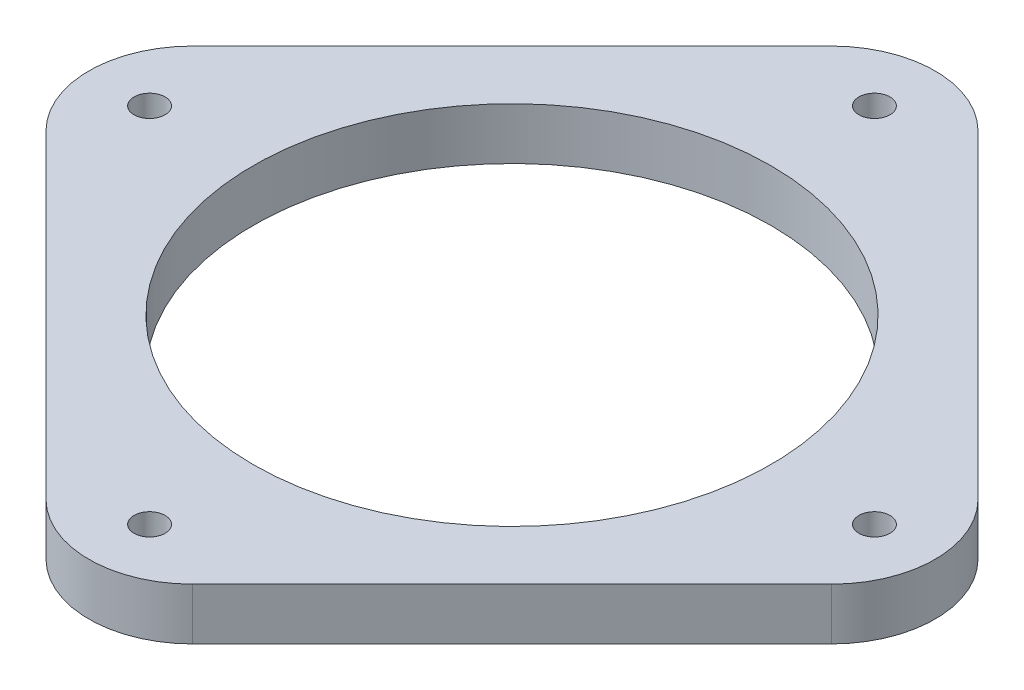
SolidWorks part; units mm, degrees
ref_plane "Alzado" through (0, 0, 0) normal (0, 0, 1) x (1, 0, 0)
ref_plane "Planta" through (0, 0, 0) normal (0, 1, 0) x (1, 0, 0)
ref_plane "Vista lateral" through (0, 0, 0) normal (1, 0, 0) x (0, 0, -1)
sketch "Croquis1" plane through (0, 0, 0) normal (0, 1, 0) x (1, 0, 0)
  line L0 (0, 0) -> (-45, 0) construction
  line L1 (-37.9289, -7.0711) -> (-7.0711, -37.9289)
  line L2 (7.0711, -37.9289) -> (37.9289, -7.0711)
  line L3 (37.9289, 7.0711) -> (7.0711, 37.9289)
  line L4 (-7.0711, 37.9289) -> (-37.9289, 7.0711)
  line L5 (0, 0) -> (35, 0) construction
  circle A0 centre (0, 0) radius 25
  circle A1 centre (0, 0) radius 31.8198 construction
  circle A2 centre (35, 0) radius 1.5
  arc A3 (-7.0711, -37.9289) -> (7.0711, -37.9289) centre (0, -30.8579) ccw
  arc A4 (-37.9289, -7.0711) -> (-37.9289, 7.0711) centre (-30.8579, 0) cw
  arc A5 (7.0711, 37.9289) -> (-7.0711, 37.9289) centre (0, 30.8579) ccw
  arc A6 (37.9289, -7.0711) -> (37.9289, 7.0711) centre (30.8579, 0) ccw
  circle A7 centre (0, -35) radius 1.5
  circle A8 centre (-35, 0) radius 1.5
  circle A9 centre (0, 35) radius 1.5
  point P19 (45, 0)
  point P29 (0, 0)
  dimension "D1" = 50
  dimension "D4" = 3
  dimension "D5" = 10
  dimension "D2" = 10
  dimension "D3" = 35
  dimension "D6" = 4
extrude "Saliente-Extruir1" add sketch "Croquis1" along normal blind 5
